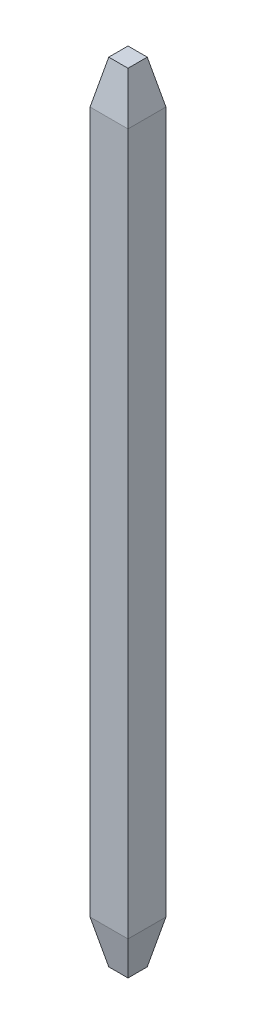
SolidWorks part; units mm, degrees
ref_plane "Front Plane" through (0, 0, 0) normal (0, 0, 1) x (1, 0, 0)
ref_plane "Top Plane" through (0, 0, 0) normal (0, 1, 0) x (1, 0, 0)
ref_plane "Right Plane" through (0, 0, 0) normal (1, 0, 0) x (0, 0, -1)
sketch "Sketch1" plane through (0, 0, 0) normal (0, 1, 0) x (1, 0, 0)
  line L1 (0, 0) -> (0.65, 0)
  line L2 (0, 0) -> (0, 0.65)
  line L3 (0, 0.65) -> (0.65, 0.65)
  line L4 (0.65, 0) -> (0.65, 0.65)
  dimension "D1" = 0.65
  dimension "D2" = 0.65
extrude "Boss-Extrude1" add sketch "Sketch1" along normal blind 13.5
chamfer "Chamfer1" distance 0.74 distance2 0.16 4 edges at (0.325, 13.5, -0.65) (0, 13.5, -0.325) (0.325, 13.5, 0) (0.65, 13.5, -0.325)
chamfer "Chamfer2" distance 0.16 distance2 0.74 4 edges at (0.325, 0, -0.65) (0.65, 0, -0.325) (0.325, 0, 0) (0, 0, -0.325)
sketch "Sketch2" plane through (0, 0, 0) normal (0, -1, 0) x (1, 0, 0)
  circle A0 centre (0.325, -0.325) radius 0.325 construction
